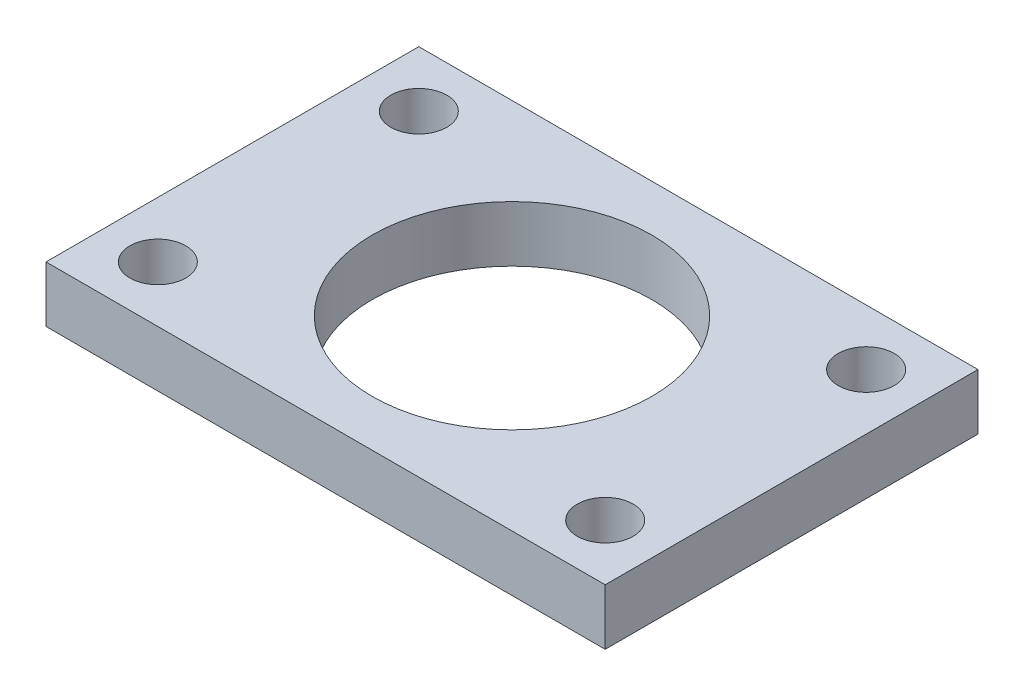
SolidWorks part; units mm, degrees
ref_plane "Front Plane" through (0, 0, 0) normal (0, 0, 1) x (1, 0, 0)
ref_plane "Top Plane" through (0, 0, 0) normal (0, 1, 0) x (1, 0, 0)
ref_plane "Right Plane" through (0, 0, 0) normal (1, 0, 0) x (0, 0, -1)
sketch "Sketch1" plane through (0, 0, 0) normal (0, 1, 0) x (1, 0, 0)
  line L1 (0, 0) -> (-30, 0)
  line L2 (0, 0) -> (0, 20)
  line L3 (0, 20) -> (-30, 20)
  line L4 (-30, 0) -> (-30, 20)
  dimension "D1" = 30
  dimension "D2" = 20
extrude "Boss-Extrude1" add sketch "Sketch1" along normal blind 3
sketch "Sketch2" plane through (0, 3, 0) normal (0, 1, 0) x (1, 0, 0)
  line L0 (0, 20) -> (-30, 20) construction
  line L1 (-30, 0) -> (0, 0) construction
  line L2 (-30, 20) -> (-30, 0) construction
  line L3 (0, 0) -> (0, 20) construction
  circle A0 centre (-27, 17) radius 1.5
  circle A1 centre (-27, 3) radius 1.5
  circle A2 centre (-3, 3) radius 1.5
  circle A3 centre (-3, 17) radius 1.5
  circle A4 centre (-15, 10) radius 7.5
  dimension "D1" = 3
  dimension "D9" = 10
  dimension "D2" = 3
  dimension "D3" = 3
  dimension "D4" = 3
  dimension "D5" = 3
  dimension "D6" = 3
  dimension "D7" = 3
  dimension "D8" = 3
  dimension "D10" = 15
extrude "Cut-Extrude1" cut sketch "Sketch2" against normal blind 23 and the other way blind 3
